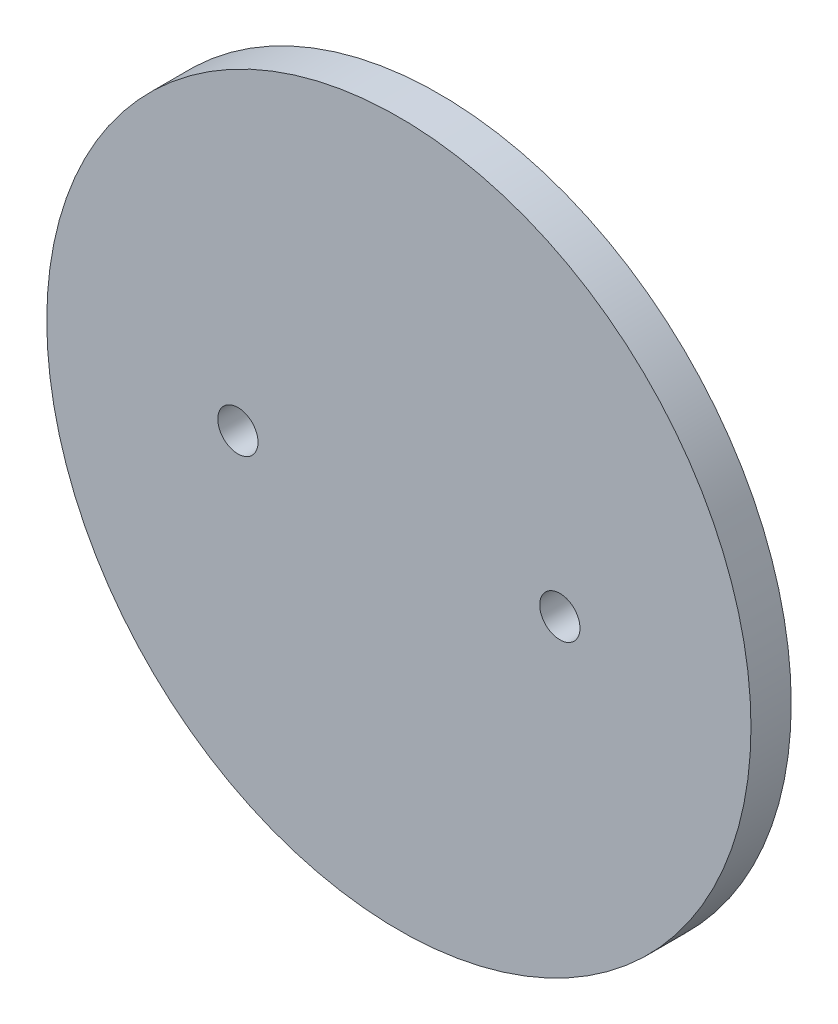
SolidWorks part; units mm, degrees
ref_plane "Front Plane" through (0, 0, 0) normal (0, 0, 1) x (1, 0, 0)
ref_plane "Top Plane" through (0, 0, 0) normal (0, 1, 0) x (1, 0, 0)
ref_plane "Right Plane" through (0, 0, 0) normal (1, 0, 0) x (0, 0, -1)
sketch "Sketch1" plane through (0, 0, 0) normal (0, 0, 1) x (1, 0, 0)
  circle A0 centre (0, 0) radius 22.225
extrude "Boss-Extrude1" add sketch "Sketch1" along normal blind 2.54
sketch "Sketch2" plane through (0, 0, 2.54) normal (0, 0, 1) x (1, 0, 0)
  line L0 (-22.225, 0) -> (22.225, 0)
  circle A0 centre (0, 0) radius 22.225 construction
  circle A1 centre (-10.16, 0) radius 1.27
  circle A2 centre (10.16, 0) radius 1.27
  point P7 (0, 0)
  dimension "D1" = 10.16
  dimension "D2" = 10.16
extrude "Cut-Extrude1" cut sketch "Sketch2" against normal through all contours L0 A1 | L0 A1 | L0 A2 | L0 A2
